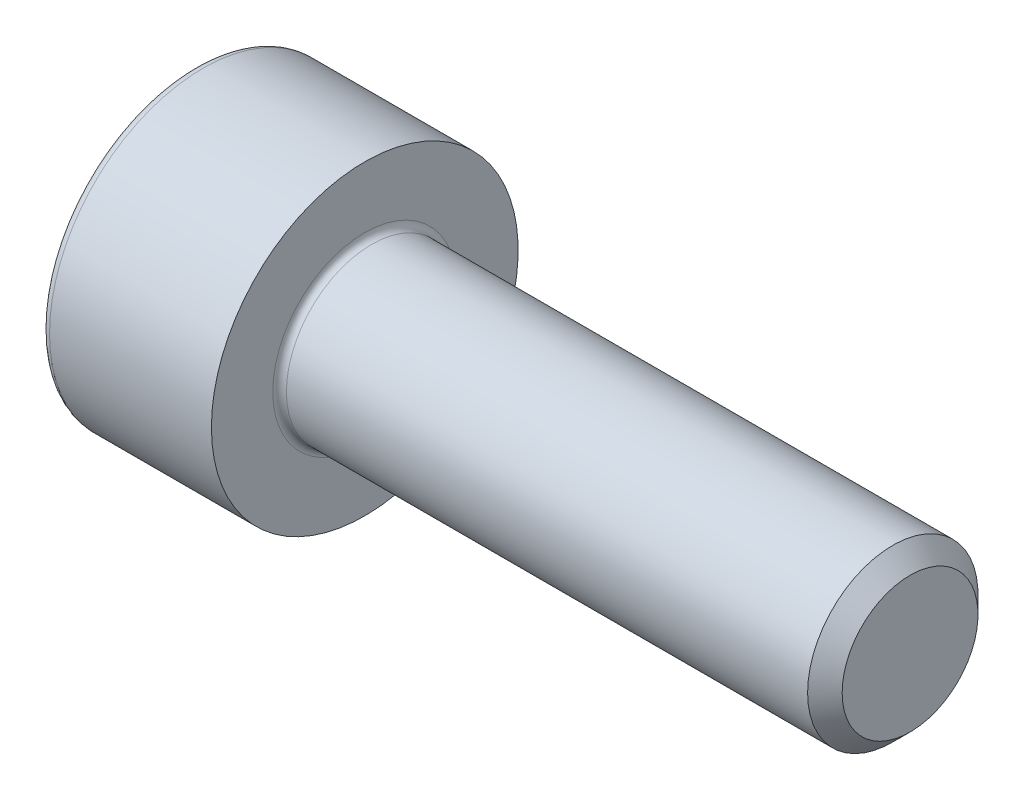
SolidWorks part; units mm, degrees
material "Aluminium"
ref_plane "Plane1" through (0, 0, 0) normal (0, 0, 1) x (1, 0, 0)
ref_plane "Plane2" through (0, 0, 0) normal (0, 1, 0) x (1, 0, 0)
ref_plane "Plane3" through (0, 0, 0) normal (1, 0, 0) x (0, 0, -1)
sketch "BodySke" plane through (0, 0, 0) normal (0, 0, 1) x (1, 0, 0)
  line L0 (0, 0) -> (0, 2.25)
  line L1 (0, 2.25) -> (2.5, 2.25)
  line L2 (2.5, 2.25) -> (2.5, 1.25)
  line L3 (2.5, 1.25) -> (10.2465, 1.25)
  line L4 (10.5, 0.9965) -> (10.5, 0)
  line L5 (10.5, 0) -> (0, 0)
  line L6 (-31.75, 0) -> (127, 0) construction
  line L8 (10.5, 0.9965) -> (10.2465, 1.25)
  line L10 (10.5, -0.9965) -> (10.2465, -1.25) construction
  line L11 (2.95, 9.525) -> (2.95, 3.175) construction
  line L12 (2.5, 9.525) -> (2.5, 3.175) construction
  line L13 (-49.5, 9.525) -> (-49.5, 3.175) construction
  dimension "Diameter" = 2.5
  dimension "Head_ht" = 2.5
  dimension "Length" = 8
  dimension "Body_ch_ang" = 45
  dimension "Head_dia" = 4.5
  dimension "Minor_dia" = 1.993
  dimension "Advance" = 0.45
  dimension "Thread_nom" = 8
  dimension "Thread_length" = 60
revolve "Base-Revolve" add sketch "BodySke"
cosmetic thread "ThreadCosmetic" [suppressed]
fillet "Fillet1" radius 0.1 1 edges at (2.5, 0, 1.25)
fillet "Fillet2" radius 0.125 1 edges at (0, 0, 2.25)
sketch "Sketch2" plane through (0, 0, 0) normal (0, 0, 1) x (1, 0, 0)
  line L0 (0, 1.0225) -> (1.1, 1.0225)
  line L1 (1.1, 1.0225) -> (1.6903, 0)
  line L2 (-31.75, 0) -> (127, 0) construction
  line L3 (1.6903, 0) -> (0, 0)
  line L4 (0, 0) -> (0, 1.0225)
  line L6 (0, 0) -> (47.625, 0) construction
  dimension "D1" = 1.0225
  dimension "D2" = 60
  dimension "Depth" = 1.1
revolve "Hex-PreBroach" cut sketch "Sketch2" angle 360 about L6
sketch "Sketch3" plane through (0, 0, 0) normal (-1, 0, 0) x (0, 0.5, 0.866)
  line L0 (0.5903, 1.0225) -> (-0.5903, 1.0225)
  line L1 (-0.5903, 1.0225) -> (-1.1807, 0)
  line L2 (0.5903, 1.0225) -> (1.1807, 0)
  line L3 (0.5903, -1.0225) -> (1.1807, 0)
  line L4 (0.5903, -1.0225) -> (-0.5903, -1.0225)
  line L5 (-0.5903, -1.0225) -> (-1.1807, 0)
  dimension "D1" = 1.0225
  dimension "D2" = 1.0225
  dimension "Hex_size" = 2.045
extrude "Hex" cut sketch "Sketch3" against normal blind 1.1
sketch "ThdSchSke" plane through (0, 0, 0) normal (0, 0, 1) x (1, 0, 0)
  line L0 (3.85, -0.9965) -> (3.6725, -1.25)
  line L1 (3.85, -0.9965) -> (4.0275, -1.25)
  line L2 (4.0275, -1.25) -> (4.0275, -1.5625)
  line L3 (-3.175, 0) -> (5.1513, 0) construction
  line L4 (0, 2.125) -> (0, -2.125) construction
  line L5 (4.0275, -1.5625) -> (3.6725, -1.5625)
  line L6 (3.6725, -1.5625) -> (3.6725, -1.25)
  dimension "Thread_minor" = 1.993
  dimension "Diameter" = 2.5
  dimension "Start" = 3.85
  dimension "SideAngle" = 55
  dimension "VeeAngle" = 70
  dimension "Overcut" = 3.125
revolve "ThreadSchematic" [suppressed] cut sketch "ThdSchSke" angle 360 about L3
pattern_linear "ThdSchPat" [suppressed]
equation "\"D2@Sketch3\" = \"Hex_size@Sketch3\" / 2"
equation "\"D1@Sketch3\" = \"Hex_size@Sketch3\" / 2"
equation "\"D1@Sketch2\" = \"Hex_size@Sketch3\" / 2"
equation "\"Thread_minor@ThreadCosmetic\"  =  \"Minor_dia@BodySke\""
equation "\"Depth@Sketch2\" =  \"Key_eng@Hex\""
equation "\"Thread_length@ThreadCosmetic\" = ((sgn( (\"Length@BodySke\" - \"Advance@BodySke\" * 3.0) - \"Thread_nom@BodySke\" )-1)*( (\"Length@BodySke\" - \"Advance@BodySke\" * 3.0) - \"Thread_nom@BodySke\" ))/-2+ \"Thread_nom@BodySke\""
equation "\"Thread_minor@ThdSchSke\" = \"Minor_dia@BodySke\""
equation "\"Diameter@ThdSchSke\" = \"Diameter@BodySke\""
equation "\"Overcut@ThdSchSke\" = \"Diameter@BodySke\" * 1.25"
equation "\"Start@ThdSchSke\" = \"Head_ht@BodySke\" + \"Length@BodySke\" - \"Thread_length@ThreadCosmetic\"  '---Non-countersunk---"
equation "\"Num_threads@ThdSchPat\" = int( \"Thread_length@ThreadCosmetic\" / \"Advance@BodySke\" + 0.999 )  + 1"
equation "\"Advance@ThdSchPat\" = \"Thread_length@ThreadCosmetic\" /  (\"Num_threads@ThdSchPat\" - 1) 'relax it"
equation "\"Num_threads@ThdSchPat\" = \"Num_threads@ThdSchPat\" - sgn( \"Num_threads@ThdSchPat\" - 1) '---chamfered tips only---"
